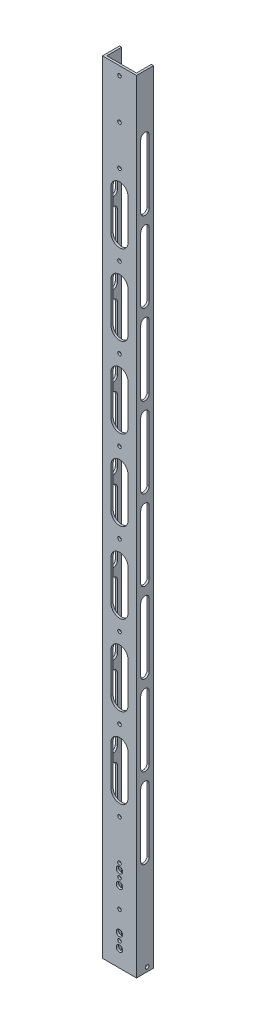
SolidWorks part; units mm, degrees
material "6061-T6 (SS)"
ref_plane "Front" through (0, 0, 0) normal (0, 0, 1) x (1, 0, 0)
ref_plane "Top" through (0, 0, 0) normal (0, 1, 0) x (1, 0, 0)
ref_plane "Right" through (0, 0, 0) normal (1, 0, 0) x (0, 0, -1)
sketch "Sketch1" plane through (0, 0, 0) normal (0, 1, 0) x (1, 0, 0)
  line L0 (3.175, 3.175) -> (3.175, 25.4)
  line L1 (0, 0) -> (50.8, 0)
  line L2 (0, 0) -> (0, 25.4)
  line L4 (50.8, 0) -> (50.8, 25.4)
  line L5 (3.175, 3.175) -> (47.625, 3.175)
  line L6 (47.625, 3.175) -> (47.625, 25.4)
  line L7 (0, 25.4) -> (3.175, 25.4)
  line L8 (50.8, 25.4) -> (47.625, 25.4)
  dimension "D1" = 25.4
  dimension "D2" = 50.8
  dimension "D3" = 3.175
extrude "Boss-Extrude1" add sketch "Sketch1" along normal blind 1168.4
sketch "Sketch2" plane through (0, 0, 0) normal (0, 0, 1) x (1, 0, 0)
  line L0 (25.4, 0) -> (25.4, 76.2) construction
  line L1 (0, 0) -> (50.8, 0) construction
  circle A0 centre (25.4, 76.2) radius 2.667
  circle A1 centre (25.4, 136.144) radius 2.667
  circle A2 centre (25.4, 196.088) radius 2.667
  circle A3 centre (25.4, 256.032) radius 2.667
  circle A4 centre (25.4, 315.976) radius 2.667
  circle A5 centre (25.4, 375.92) radius 2.667
  circle A6 centre (25.4, 435.864) radius 2.667
  circle A7 centre (25.4, 495.808) radius 2.667
  circle A8 centre (25.4, 555.752) radius 2.667
  circle A11 centre (25.4, 615.696) radius 2.667
  circle A12 centre (25.4, 675.64) radius 2.667
  circle A13 centre (25.4, 735.584) radius 2.667
  circle A14 centre (25.4, 795.528) radius 2.667
  circle A15 centre (25.4, 855.472) radius 2.667
  circle A16 centre (25.4, 915.416) radius 2.667
  circle A17 centre (25.4, 975.36) radius 2.667
  circle A18 centre (25.4, 1035.304) radius 2.667
  circle A19 centre (25.4, 1095.248) radius 2.667
  circle A20 centre (25.4, 1155.192) radius 2.667
  dimension "D2" = 5.334
  dimension "D1" = 76.2
  dimension "D3" = 19
extrude "Igus_Holes" cut sketch "Sketch2" against normal up to next
sketch "Sketch3" plane through (0, 0, -3.175) normal (0, 0, -1) x (-1, 0, 0)
  line L0 (-25.4, 0) -> (-25.4, 25.4) construction
  line L1 (-47.625, 0) -> (-3.175, 0) construction
  circle A0 centre (-25.4, 25.4) radius 4.7625
  circle A8 centre (-25.4, 35.4) radius 2.667
  circle A9 centre (-25.4, 117) radius 2.667
  circle A10 centre (-25.4, 45.4) radius 4.7625 construction
  circle A11 centre (-25.4, 45.4) radius 4.7625
  circle A12 centre (-25.4, 107) radius 4.7625 construction
  circle A13 centre (-25.4, 107) radius 4.7625
  circle A14 centre (-25.4, 127) radius 4.7625 construction
  circle A15 centre (-25.4, 127) radius 4.7625
  dimension "D2" = 9.525
  dimension "D4" = 5.334
  dimension "D3" = 5.334
  dimension "D1" = 25.4
extrude "Cut-Extrude2" cut sketch "Sketch3" against normal up to next
sketch "Sketch4" plane through (0, 0, 0) normal (-1, 0, 0) x (0, 0, 1)
  line L0 (-15.875, 0) -> (-15.875, 6.35) construction
  line L2 (-25.4, 0) -> (0, 0) construction
  line L3 (-15.875, 6.35) -> (-25.4, 6.35) construction
  line L4 (-25.4, 1168.4) -> (-25.4, 0) construction
  circle A0 centre (-15.875, 6.35) radius 2.667
  dimension "D2" = 5.334
  dimension "D1" = 6.35
  dimension "D3" = 9.525
extrude "Cut-Extrude3" cut sketch "Sketch4" against normal through all
ref_plane "Mid_Plane" through (25.4, 0, 0) normal (1, 0, 0) x (0, 0, -1)
sketch "Sketch5" plane through (0, 0, 0) normal (0, 0, 1) x (1, 0, 0)
  line L0 (25.4, 1005.36) -> (25.4, 945.36) construction
  line L1 (38.1, 1005.36) -> (38.1, 945.36)
  line L2 (12.7, 1005.36) -> (12.7, 945.36)
  line L4 (0, 1168.4) -> (0, 0) construction
  line L5 (25.4, 885.472) -> (25.4, 825.472) construction
  line L6 (38.1, 885.472) -> (38.1, 825.472)
  line L7 (12.7, 885.472) -> (12.7, 825.472)
  line L8 (25.4, 765.584) -> (25.4, 705.584) construction
  line L9 (38.1, 765.584) -> (38.1, 705.584)
  line L10 (12.7, 765.584) -> (12.7, 705.584)
  line L11 (25.4, 645.696) -> (25.4, 585.696) construction
  line L12 (38.1, 645.696) -> (38.1, 585.696)
  line L13 (12.7, 645.696) -> (12.7, 585.696)
  line L14 (25.4, 525.808) -> (25.4, 465.808) construction
  line L15 (38.1, 525.808) -> (38.1, 465.808)
  line L16 (12.7, 525.808) -> (12.7, 465.808)
  line L17 (25.4, 405.92) -> (25.4, 345.92) construction
  line L18 (38.1, 405.92) -> (38.1, 345.92)
  line L19 (12.7, 405.92) -> (12.7, 345.92)
  line L20 (25.4, 286.032) -> (25.4, 226.032) construction
  line L21 (38.1, 286.032) -> (38.1, 226.032)
  line L22 (12.7, 286.032) -> (12.7, 226.032)
  arc A0 (38.1, 1005.36) -> (12.7, 1005.36) centre (25.4, 1005.36) ccw
  arc A1 (12.7, 945.36) -> (38.1, 945.36) centre (25.4, 945.36) ccw
  circle A2 centre (25.4, 975.36) radius 2.667 construction
  circle A3 centre (25.4, 975.36) radius 2.667 construction
  arc A4 (38.1, 885.472) -> (12.7, 885.472) centre (25.4, 885.472) ccw
  arc A5 (12.7, 825.472) -> (38.1, 825.472) centre (25.4, 825.472) ccw
  arc A6 (38.1, 765.584) -> (12.7, 765.584) centre (25.4, 765.584) ccw
  arc A7 (12.7, 705.584) -> (38.1, 705.584) centre (25.4, 705.584) ccw
  arc A8 (38.1, 645.696) -> (12.7, 645.696) centre (25.4, 645.696) ccw
  arc A9 (12.7, 585.696) -> (38.1, 585.696) centre (25.4, 585.696) ccw
  arc A10 (38.1, 525.808) -> (12.7, 525.808) centre (25.4, 525.808) ccw
  arc A11 (12.7, 465.808) -> (38.1, 465.808) centre (25.4, 465.808) ccw
  arc A12 (38.1, 405.92) -> (12.7, 405.92) centre (25.4, 405.92) ccw
  arc A13 (12.7, 345.92) -> (38.1, 345.92) centre (25.4, 345.92) ccw
  arc A14 (38.1, 286.032) -> (12.7, 286.032) centre (25.4, 286.032) ccw
  arc A15 (12.7, 226.032) -> (38.1, 226.032) centre (25.4, 226.032) ccw
  point P2 (25.4, 975.36)
  point P16 (25.4, 855.472)
  point P23 (25.4, 735.584)
  point P30 (25.4, 615.696)
  point P37 (25.4, 495.808)
  point P44 (25.4, 375.92)
  point P51 (25.4, 256.032)
  dimension "D3" = 30
  dimension "D4" = 30
  dimension "D1" = 25.4
  dimension "D2" = 12.7
extrude "Back_Cuts" cut sketch "Sketch5" against normal up to next
sketch "Sketch6" plane through (0, 0, 0) normal (-1, 0, 0) x (0, 0, 1)
  line L0 (-12.7, 1082.05) -> (-12.7, 987.25) construction
  line L1 (-6.35, 1082.05) -> (-6.35, 987.25)
  line L2 (-19.05, 1082.05) -> (-19.05, 987.25)
  line L3 (-25.4, 1168.4) -> (-25.4, 0) construction
  line L4 (-25.4, 1168.4) -> (0, 1168.4) construction
  line L5 (-12.7, 962.05) -> (-12.7, 867.25) construction
  line L6 (-6.35, 962.05) -> (-6.35, 867.25)
  line L7 (-19.05, 962.05) -> (-19.05, 867.25)
  line L8 (-12.7, 842.05) -> (-12.7, 747.25) construction
  line L9 (-6.35, 842.05) -> (-6.35, 747.25)
  line L10 (-19.05, 842.05) -> (-19.05, 747.25)
  line L11 (-12.7, 722.05) -> (-12.7, 627.25) construction
  line L12 (-6.35, 722.05) -> (-6.35, 627.25)
  line L13 (-19.05, 722.05) -> (-19.05, 627.25)
  line L14 (-12.7, 602.05) -> (-12.7, 507.25) construction
  line L15 (-6.35, 602.05) -> (-6.35, 507.25)
  line L16 (-19.05, 602.05) -> (-19.05, 507.25)
  line L17 (-12.7, 482.05) -> (-12.7, 387.25) construction
  line L18 (-6.35, 482.05) -> (-6.35, 387.25)
  line L19 (-19.05, 482.05) -> (-19.05, 387.25)
  line L20 (-12.7, 362.05) -> (-12.7, 267.25) construction
  line L21 (-6.35, 362.05) -> (-6.35, 267.25)
  line L22 (-19.05, 362.05) -> (-19.05, 267.25)
  line L23 (-12.7, 242.05) -> (-12.7, 147.25) construction
  line L24 (-6.35, 242.05) -> (-6.35, 147.25)
  line L25 (-19.05, 242.05) -> (-19.05, 147.25)
  arc A0 (-6.35, 1082.05) -> (-19.05, 1082.05) centre (-12.7, 1082.05) ccw
  arc A1 (-19.05, 987.25) -> (-6.35, 987.25) centre (-12.7, 987.25) ccw
  arc A2 (-6.35, 962.05) -> (-19.05, 962.05) centre (-12.7, 962.05) ccw
  arc A3 (-19.05, 867.25) -> (-6.35, 867.25) centre (-12.7, 867.25) ccw
  arc A4 (-6.35, 842.05) -> (-19.05, 842.05) centre (-12.7, 842.05) ccw
  arc A5 (-19.05, 747.25) -> (-6.35, 747.25) centre (-12.7, 747.25) ccw
  arc A6 (-6.35, 722.05) -> (-19.05, 722.05) centre (-12.7, 722.05) ccw
  arc A7 (-19.05, 627.25) -> (-6.35, 627.25) centre (-12.7, 627.25) ccw
  arc A8 (-6.35, 602.05) -> (-19.05, 602.05) centre (-12.7, 602.05) ccw
  arc A9 (-19.05, 507.25) -> (-6.35, 507.25) centre (-12.7, 507.25) ccw
  arc A10 (-6.35, 482.05) -> (-19.05, 482.05) centre (-12.7, 482.05) ccw
  arc A11 (-19.05, 387.25) -> (-6.35, 387.25) centre (-12.7, 387.25) ccw
  arc A12 (-6.35, 362.05) -> (-19.05, 362.05) centre (-12.7, 362.05) ccw
  arc A13 (-19.05, 267.25) -> (-6.35, 267.25) centre (-12.7, 267.25) ccw
  arc A14 (-6.35, 242.05) -> (-19.05, 242.05) centre (-12.7, 242.05) ccw
  arc A15 (-19.05, 147.25) -> (-6.35, 147.25) centre (-12.7, 147.25) ccw
  point P2 (-12.7, 1034.65)
  point P7 (-12.7, 1088.4)
  point P8 (-12.7, 980.9)
  point P17 (-12.7, 914.65)
  point P24 (-12.7, 794.65)
  point P29 (-12.7, 674.65)
  point P36 (-12.7, 554.65)
  point P43 (-12.7, 434.65)
  point P50 (-12.7, 314.65)
  point P57 (-12.7, 194.65)
  point P62 (-12.7, 968.4)
  dimension "D1" = 12.7
  dimension "D2" = 107.5
  dimension "D3" = 6.35
  dimension "D4" = 80
  dimension "D6" = 12.5
  dimension "D5" = 8
extrude "Cut-Extrude5" cut sketch "Sketch6" against normal through all
sketch "Sketch7" plane through (0, 0, 0) normal (0, 0, 1) x (1, 0, 0)
  line L0 (28.067, 196.088) -> (50.8, 196.088) construction
  line L1 (50.8, 1168.4) -> (50.8, 0) construction
  line L2 (22.733, 196.088) -> (0, 196.088) construction
  line L3 (0, 1168.4) -> (0, 0) construction
  circle A0 centre (25.4, 196.088) radius 2.667 construction
sketch "Sketch8" plane through (0, 0, 0) normal (-1, 0, 0) x (0, 0, 1)
  line L0 (0, 196.088) -> (-6.35, 196.088) construction
  line L1 (-6.35, 147.25) -> (-6.35, 242.05) construction
sketch "Sketch9" plane through (0, 0, 0) normal (0, 0, 1) x (1, 0, 0)
  line L0 (25.4, 298.732) -> (25.4, 315.976) construction
  arc A0 (38.1, 286.032) -> (12.7, 286.032) centre (25.4, 286.032) ccw construction
  dimension "D1" = 17.244
